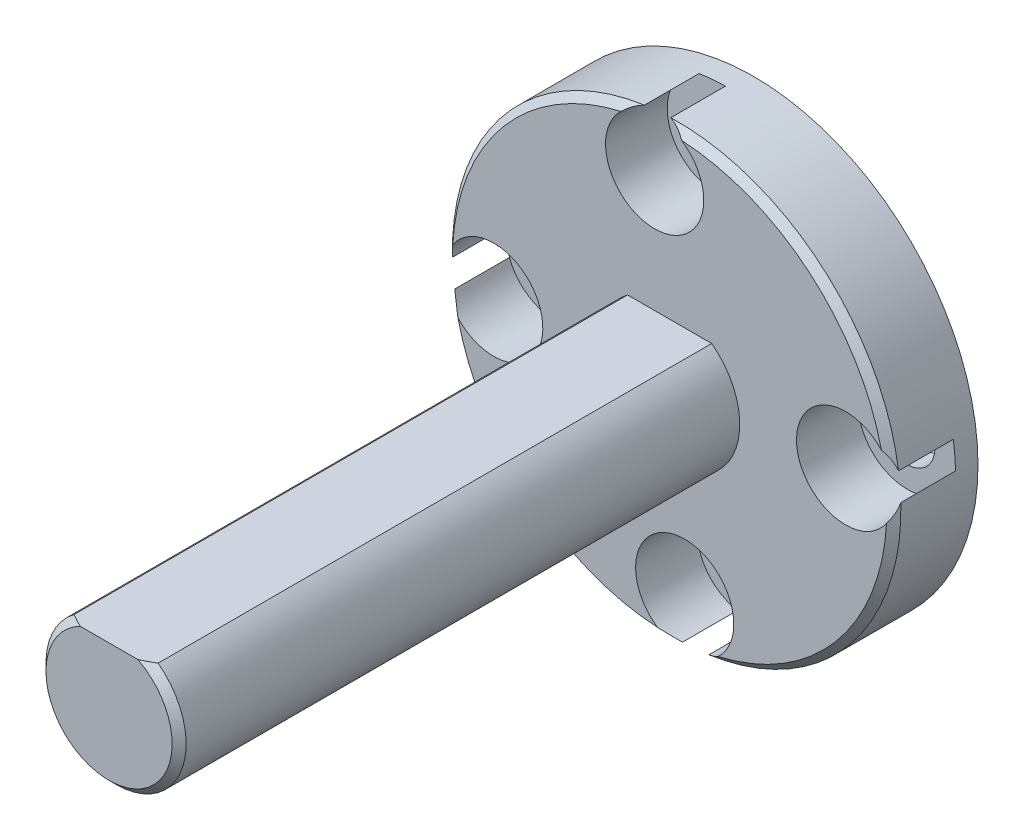
SolidWorks part; units mm, degrees
material "ABS"
ref_plane "Plan de face" through (0, 0, 0) normal (0, 0, 1) x (1, 0, 0)
ref_plane "Plan de dessus" through (0, 0, 0) normal (0, 1, 0) x (1, 0, 0)
ref_plane "Plan de droite" through (0, 0, 0) normal (1, 0, 0) x (0, 0, -1)
sketch "Esquisse1" plane through (0, 0, 0) normal (0, 0, 1) x (1, 0, 0)
  line L0 (0.6185, -20.175) -> (0.6185, 0.145) construction
  line L1 (-9.5415, -10.015) -> (10.7785, -10.015) construction
  circle A0 centre (0.6185, -10.015) radius 10.16
  circle A1 centre (8.5895, -9.3345) radius 1.25
  circle A2 centre (1.2989, -17.986) radius 1.25
  circle A3 centre (-7.3526, -10.6955) radius 1.25
  circle A4 centre (-0.062, -2.044) radius 1.25
  dimension "D1" = 2.5
  dimension "D2" = 20.32
  dimension "D3" = 2.5
  dimension "D4" = 2.5
  dimension "D5" = 2.5
extrude "Boss.-Extru.2" add sketch "Esquisse1" along normal blind 3.81
sketch "Esquisse2" plane through (0, 0, 3.81) normal (0, 0, 1) x (1, 0, 0)
  line L0 (0.6185, 0.145) -> (0.6185, -20.175) construction
  line L1 (-9.5415, -10.015) -> (10.7785, -10.015) construction
  line L2 (-1.2865, -7.475) -> (2.5235, -7.475)
  circle A0 centre (0.6185, -10.015) radius 10.16 construction
  arc A1 (-1.2865, -7.475) -> (2.5235, -7.475) centre (0.6185, -10.015) ccw
  dimension "D1" = 6.35
  dimension "D2" = 3.81
extrude "Boss.-Extru.3" add sketch "Esquisse2" along normal blind 25.4
chamfer "Chanfrein1" distance 0.3175 angle 45 2 edges at (10.7785, -10.015, 3.81) (0.6185, -13.19, 29.21)
sketch "Esquisse3" plane through (0, 0, 0) normal (0, 0, -1) x (-1, 0, 0)
  line L0 (-0.6185, 0.145) -> (-0.6185, -20.175) construction
  line L1 (-10.7785, -10.015) -> (9.5415, -10.015) construction
  circle A0 centre (-0.6185, -10.015) radius 10.16 construction
  circle A1 centre (-0.6185, -10.015) radius 4.445
  dimension "D1" = 8.89
extrude "Enlèv. mat.-Extru.1" cut sketch "Esquisse3" against normal blind 2.54
sketch "Esquisse4" plane through (0, 0, 3.81) normal (0, 0, 1) x (1, 0, 0)
  circle A0 centre (-0.062, -2.044) radius 2.2245
  circle A1 centre (8.5895, -9.3345) radius 2.2245
  circle A2 centre (1.2989, -17.986) radius 2.2245
  circle A3 centre (-7.3526, -10.6955) radius 2.2245
extrude "Enlèv. mat.-Extru.6" cut sketch "Esquisse4" against normal blind 2.794
